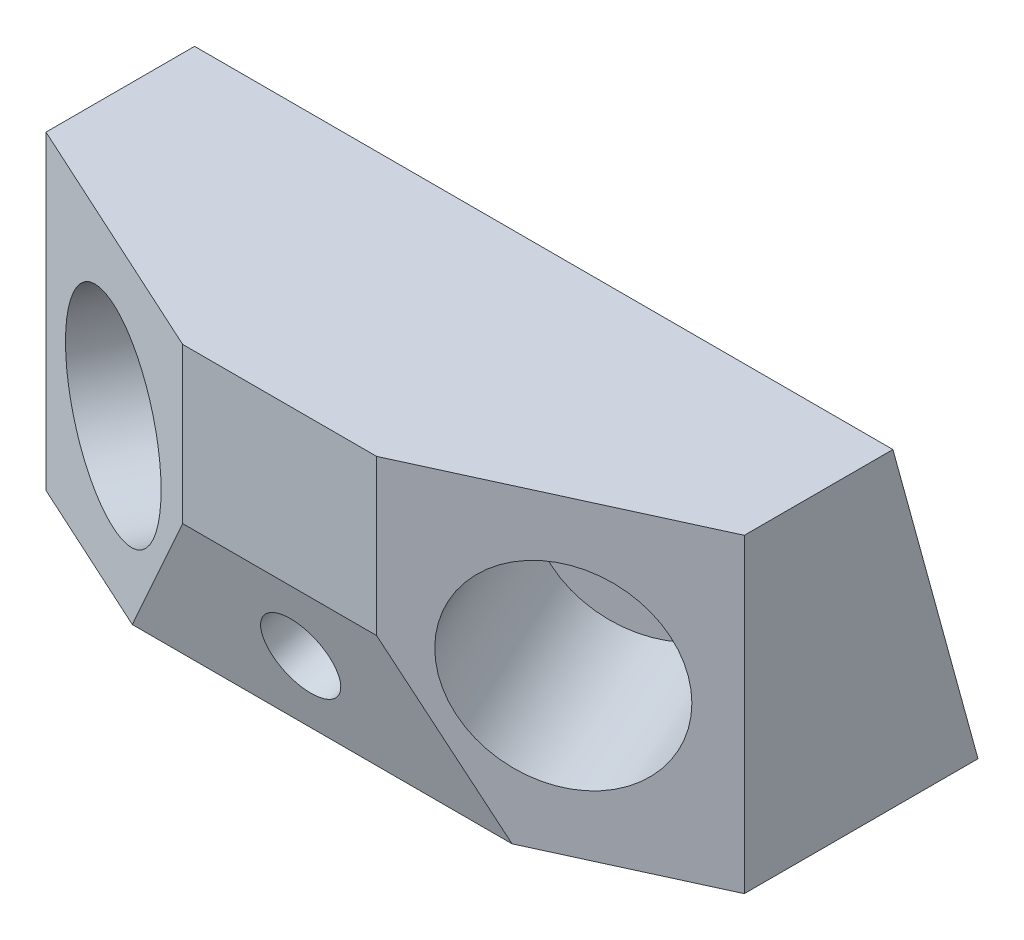
SolidWorks part; units mm, degrees
material "3.0255 (EN-AW 1350A)"
ref_plane "Plan de face" through (0, 0, 0) normal (0, 0, 1) x (1, 0, 0)
ref_plane "Plan de dessus" through (0, 0, 0) normal (0, 1, 0) x (1, 0, 0)
ref_plane "Plan de droite" through (0, 0, 0) normal (1, 0, 0) x (0, 0, -1)
sketch "Esquisse1" plane through (0, 0, 0) normal (0, 0, 1) x (1, 0, 0)
  line L1 (-45, -20) -> (45, -20)
  line L2 (-45, -20) -> (-45, 20)
  line L3 (-45, 20) -> (45, 20)
  line L4 (45, -20) -> (45, 20)
  line L5 (-45, -20) -> (45, 20) construction
  line L6 (-45, 20) -> (45, -20) construction
  point P0 (0, 0)
  dimension "D1" = 90
  dimension "D2" = 40
extrude "Boss.-Extru.1" add sketch "Esquisse1" along normal blind 45
sketch "Esquisse2" plane through (0, -20, 0) normal (0, -1, 0) x (1, 0, 0)
  line L0 (-12.5, 45) -> (12.5, 45)
  line L1 (-45, 45) -> (45, 45) construction
  line L2 (-12.5, 45) -> (-45, 30.1135)
  line L3 (-45, 45) -> (-45, 0) construction
  line L4 (12.5, 45) -> (45, 30.1135)
  line L5 (45, 45) -> (45, 0) construction
  line L6 (-45, 30.1135) -> (-45, 45)
  line L7 (-45, 45) -> (-12.5, 45)
  line L8 (-45, 45) -> (-12.5, 45)
  line L9 (45, 30.1135) -> (45, 45)
  line L10 (45, 45) -> (12.5, 45)
  point P5 (0, 45)
  line M5 (45, 0) -> (45, 45)
  line M6 (45, 45) -> (-45, 45)
  line M7 (-45, 45) -> (-45, 0)
  dimension "D1" = 25
  dimension "D2" = 24.61
  dimension "D3" = 24.61
extrude "Enlèv. mat.-Extru.2" cut sketch "Esquisse2" against normal blind 45 contours L4 M6 M5 | L2 M6 M7
sketch "Esquisse3" plane through (45, 0, 0) normal (1, 0, 0) x (0, 0, -1)
  line L0 (0, -20) -> (-10.9653, 20)
  line L1 (-30.1135, 20) -> (0, 20) construction
  line L2 (-10.9653, 20) -> (0, 20)
  line L3 (0, 20) -> (0, -20)
  line L4 (-45, 0) -> (-39.5174, -20)
  line L5 (-45, -20) -> (-45, 20) construction
  line L6 (-45, -20) -> (-30.1135, -20) construction
  line L7 (-45, 0) -> (-45, -20)
  line L8 (-45, -20) -> (-39.5174, -20)
  dimension "D1" = 15.33
extrude "Enlèv. mat.-Extru.3" cut sketch "Esquisse3" against normal blind 106
sketch "Esquisse6" plane through (19.2053, 0, 41.9287) normal (0.4164, 0, 0.9092) x (0.9092, 0, -0.4164)
  line L0 (-7.3752, 20) -> (28.3719, 20) construction
  line L1 (28.3719, 20) -> (28.3719, -20) construction
  circle A0 centre (10.7719, 0) radius 12.5
  dimension "D1" = 25
  dimension "D2" = 20
  dimension "D3" = 17.6
extrude "Enlèv. mat.-Extru.4" cut sketch "Esquisse6" against normal blind 25
mirror "Symétrie1" about plane through (0, 0, 0) normal (1, 0, 0) of "Enlèv. mat.-Extru.4"
sketch "Esquisse7" plane through (0, -11.4737, 41.8547) normal (0, -0.2644, 0.9644) x (1, 0, 0)
  line L0 (-24.4696, -8.8409) -> (24.4696, -8.8409) construction
  line L1 (0, -8.8409) -> (0, 11.897) construction
  line L2 (-12.5, 11.897) -> (12.5, 11.897) construction
  circle A0 centre (0, 1.6591) radius 5
  dimension "D1" = 10
  dimension "D2" = 10.5
extrude "Enlèv. mat.-Extru.5" cut sketch "Esquisse7" against normal blind 56
sketch "Esquisse8" plane through (0, -1.3979, 5.0994) normal (0, 0.2644, -0.9644) x (-1, 0, 0)
  point P0 (0, 1.6591)
sketch "Esquisse9" plane through (0, -1.3979, 5.0994) normal (0, 0.2644, -0.9644) x (-1, 0, 0)
  line L0 (0, 1.6591) -> (45, 1.4495) construction
  line L3 (45, 22.1874) -> (45, -19.2884) construction
  line L4 (45, 1.4495) -> (-45, 1.8688) construction
  line L5 (-45, 22.1874) -> (-45, -19.2884) construction
  circle A0 centre (35, 1.4961) radius 2
  circle A1 centre (-35, 1.8222) radius 2
  dimension "D1" = 4
  dimension "D2" = 4
  dimension "D3" = 35
  dimension "D4" = 35
extrude "Enlèv. mat.-Extru.6" cut sketch "Esquisse9" against normal blind 11
